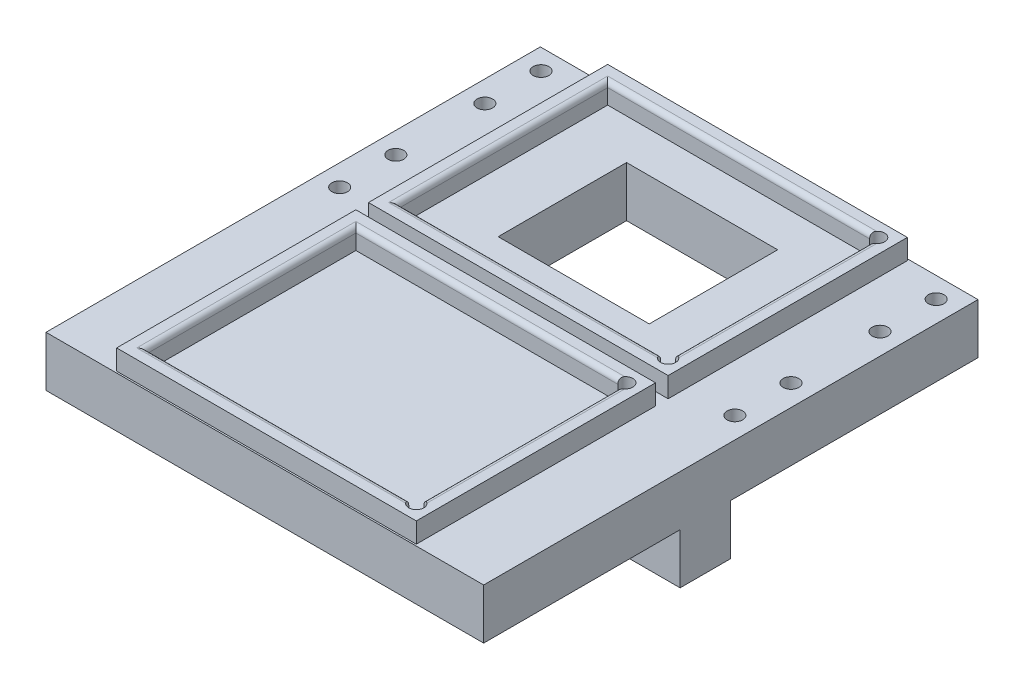
SolidWorks part; units mm, degrees
ref_plane "Front Plane" through (0, 0, 0) normal (0, 0, 1) x (1, 0, 0)
ref_plane "Top Plane" through (0, 0, 0) normal (0, 1, 0) x (1, 0, 0)
ref_plane "Right Plane" through (0, 0, 0) normal (1, 0, 0) x (0, 0, -1)
sketch "Sketch1" plane through (0, 0, 0) normal (0, 1, 0) x (1, 0, 0)
  line L0 (0, 0) -> (0, -50000) construction
  line L1 (-43.45, 24.075) -> (43.45, 24.075)
  line L2 (-43.45, 24.075) -> (-43.45, -24.075)
  line L3 (-43.45, -24.075) -> (43.45, -24.075) construction
  line L4 (43.45, 24.075) -> (43.45, -24.075)
  line L5 (-43.45, 24.075) -> (43.45, -24.075) construction
  line L6 (-43.45, -24.075) -> (43.45, 24.075) construction
  line L7 (-43.45, -24.075) -> (-43.45, -74.075)
  line L8 (-15, 12.75) -> (15, 12.75)
  line L9 (-15, 12.75) -> (-15, -12.75)
  line L10 (-15, -12.75) -> (15, -12.75)
  line L11 (15, 12.75) -> (15, -12.75)
  line L12 (-15, 12.75) -> (15, -12.75) construction
  line L13 (-15, -12.75) -> (15, 12.75) construction
  line L22 (-43.45, -74.075) -> (43.45, -74.075)
  line L23 (43.45, -74.075) -> (43.45, -24.075)
  circle A0 centre (-39.23, 19.985) radius 1.55
  circle A1 centre (-39.23, 8.835) radius 1.55
  circle A2 centre (-39.23, -8.835) radius 1.55
  circle A3 centre (-39.23, -19.985) radius 1.55
  circle A4 centre (39.23, -19.985) radius 1.55
  circle A5 centre (39.23, -8.835) radius 1.55
  circle A6 centre (39.23, 8.835) radius 1.55
  circle A7 centre (39.23, 19.985) radius 1.55
  point P0 (0, 0)
  point P24 (0, 0)
  dimension "D3" = 3.1
  dimension "D4" = 4.22
  dimension "D5" = 4.09
  dimension "D6" = 11.15
  dimension "D7" = 17.67
  dimension "D8" = 11.15
  dimension "D9" = 4.22
  dimension "D10" = 4.22
  dimension "D11" = 4.22
  dimension "D1" = 48.15
  dimension "D2" = 86.9
  dimension "D12" = 30
  dimension "D13" = 25.5
  dimension "D14" = 50
extrude "Boss-Extrude1" add sketch "Sketch1" along normal blind 10
sketch "Sketch2" plane through (0, 10, 0) normal (0, 1, 0) x (1, 0, 0)
  line L0 (29.75, -26.25) -> (29.75, -73.75)
  line L1 (-26, 20) -> (26, 20) construction
  line L2 (-26, 20) -> (-26, -20) construction
  line L3 (-26, -20) -> (26, -20) construction
  line L4 (26, 20) -> (26, -20) construction
  line L5 (-26, 20) -> (26, -20) construction
  line L6 (-26, -20) -> (26, 20) construction
  line L7 (-26.75, 20.75) -> (26.75, 20.75)
  line L8 (-26.75, 20.75) -> (-26.75, -20.75)
  line L9 (-26.75, -20.75) -> (26.75, -20.75)
  line L10 (26.75, 20.75) -> (26.75, -20.75)
  line L11 (-26.75, 20.75) -> (26.75, -20.75) construction
  line L12 (-26.75, -20.75) -> (26.75, 20.75) construction
  line L13 (-29.75, 23.75) -> (29.75, 23.75)
  line L14 (-29.75, 23.75) -> (-29.75, -23.75)
  line L15 (-29.75, -23.75) -> (29.75, -23.75)
  line L16 (29.75, 23.75) -> (29.75, -23.75)
  line L17 (-29.75, 23.75) -> (29.75, -23.75) construction
  line L18 (-29.75, -23.75) -> (29.75, 23.75) construction
  line L19 (-26.75, -29.25) -> (-26.75, -70.75)
  line L20 (-26.75, -29.25) -> (26.75, -29.25)
  line L21 (26.75, -29.25) -> (26.75, -70.75)
  line L22 (-26.75, -70.75) -> (26.75, -70.75)
  line L23 (-29.75, -26.25) -> (-29.75, -73.75)
  line L24 (-29.75, -26.25) -> (29.75, -26.25)
  line L25 (-29.75, -73.75) -> (29.75, -73.75)
  point P0 (0, 0)
  point P6 (0, 0)
  point P11 (0, 0)
  dimension "D1" = 52
  dimension "D2" = 40
  dimension "D3" = 41.5
  dimension "D4" = 53.5
  dimension "D5" = 3
  dimension "D6" = 3
  dimension "D7" = 2
extrude "Boss-Extrude2" add sketch "Sketch2" along normal blind 4
sketch "Sketch3" plane through (0, 14, 0) normal (0, 1, 0) x (1, 0, 0)
  circle A0 centre (26.75, 20.75) radius 1.5
  circle A1 centre (26.75, -20.75) radius 1.5
  circle A2 centre (26.75, -29.25) radius 1.5
  circle A3 centre (26.75, -70.75) radius 1.5
  dimension "D1" = 3
  dimension "D2" = 3
extrude "Cut-Extrude1" cut sketch "Sketch3" against normal up to next
fillet "Fillet2" radius 1 8 edges at (26.75, 14, 0) (-0.75, 14, 20.75) (-26.75, 14, 0) (-0.75, 14, -20.75) (-0.75, 14, 70.75) (26.75, 14, 50) (-0.75, 14, 29.25) (-26.75, 14, 50)
sketch "Sketch6" plane through (0, 0, 0) normal (0, -1, 0) x (1, 0, 0)
  line L0 (43.45, 74.075) -> (43.45, -24.075) construction
  line L1 (-43.45, 74.075) -> (43.45, 74.075) construction
  line L2 (-43.45, 74.075) -> (-43.45, 25.075) construction
  line L3 (-43.45, 25.075) -> (43.45, 25.075) construction
  line L4 (43.45, 74.075) -> (43.45, 25.075) construction
  line L6 (-43.45, 25.075) -> (43.45, 25.075)
  line L7 (-43.45, 25.075) -> (-43.45, 35.075)
  line L8 (-43.45, 35.075) -> (43.45, 35.075)
  line L9 (43.45, 25.075) -> (43.45, 35.075)
  dimension "D1" = 49
  dimension "D2" = 10
extrude "Boss-Extrude3" add sketch "Sketch6" along normal blind 10
sketch "Sketch7" plane through (0, 0, 35.075) normal (0, 0, 1) x (1, 0, 0)
  line L0 (0, 0) -> (0, -10) construction
  line L1 (-43.45, 0) -> (43.45, 0) construction
  line L2 (-43.45, 0) -> (-43.45, -10) construction
  line L3 (-43.45, -10) -> (43.45, -10) construction
  line L4 (43.45, 0) -> (43.45, -10) construction
  circle A0 centre (-33.45, -5) radius 1.55
  circle A1 centre (33.45, -5) radius 1.55
  dimension "D1" = 10
  dimension "D2" = 5
  dimension "D3" = 3.1
extrude "Cut-Extrude2" cut sketch "Sketch7" against normal up to next
